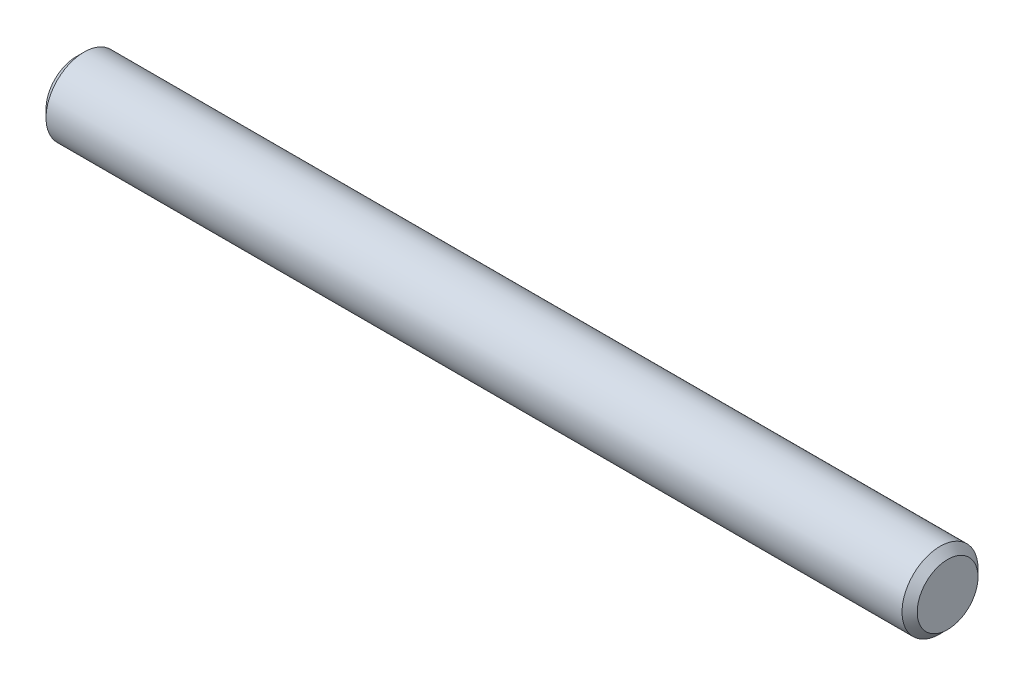
SolidWorks part; units mm, degrees
ref_plane "Front" through (0, 0, 0) normal (0, 0, 1) x (1, 0, 0)
ref_plane "Top" through (0, 0, 0) normal (0, 1, 0) x (1, 0, 0)
ref_plane "Right" through (0, 0, 0) normal (1, 0, 0) x (0, 0, -1)
sketch "Sketch1" plane through (0, 0, 0) normal (0, 0, 1) x (1, 0, 0)
  line L0 (-27.305, 0) -> (27.305, 0) construction
  line L1 (27.305, 2.3813) -> (27.305, -2.3813) construction
  line L2 (-27.305, 2.3813) -> (-27.305, -2.3813) construction
  dimension "Length" = 54.61
  dimension "Diameter" = 4.7625
sketch "Sketch2" plane through (0, 0, 0) normal (1, 0, 0) x (0, 0, -1)
  circle A0 centre (0, 0) radius 2.3813
extrude "Extrude1" add sketch "Sketch2" against normal up to vertex (27.305 mm away) and the other way up to vertex (27.305 mm away) up to point (-27.305, 2.3813, 0) other way up to point (27.305, 2.3813, 0)
chamfer "Chamfer1" distance 0.4763 angle 45 2 edges at (27.305, 0, -2.3813) (-27.305, 0, -2.3813)
equation "\"D1@Chamfer1\" = \"Diameter@Sketch1\"*.1"
